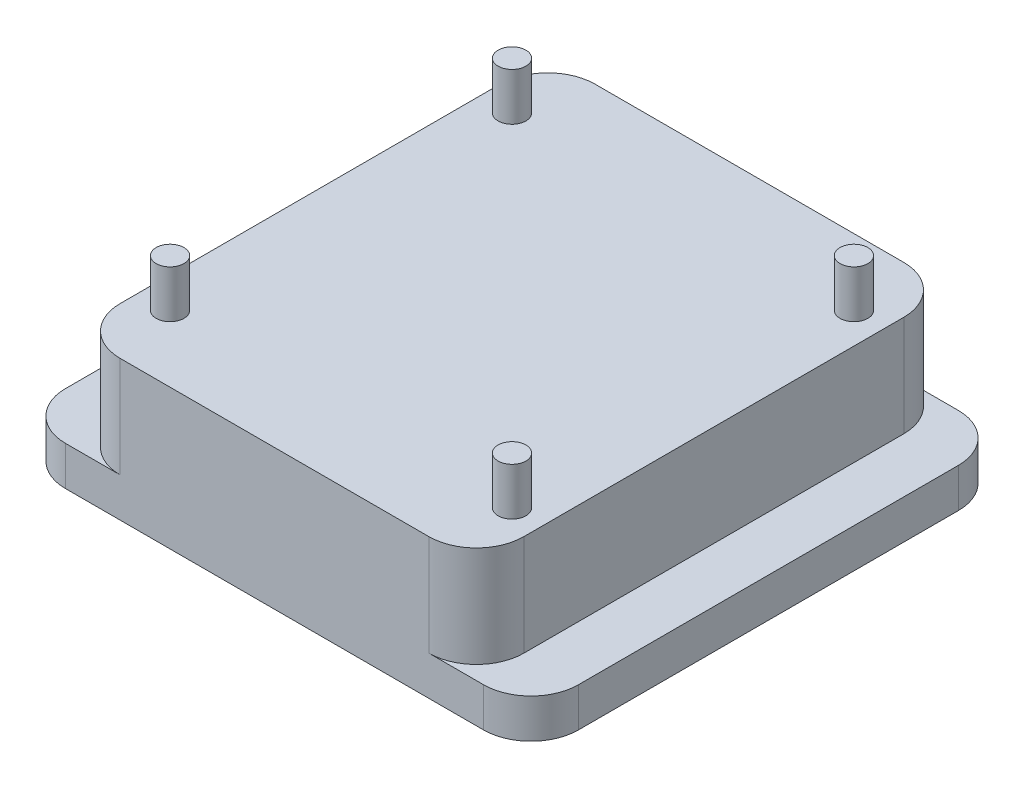
SolidWorks part; units mm, degrees
ref_plane "Front Plane" through (0, 0, 0) normal (0, 0, 1) x (1, 0, 0)
ref_plane "Top Plane" through (0, 0, 0) normal (0, 1, 0) x (1, 0, 0)
ref_plane "Right Plane" through (0, 0, 0) normal (1, 0, 0) x (0, 0, -1)
sketch "Sketch1" plane through (0, 0, 0) normal (0, 0, 1) x (1, 0, 0)
  line L1 (-27.432, -2.0955) -> (27.432, -2.0955)
  line L2 (-27.432, -2.0955) -> (-27.432, 2.0955)
  line L3 (-27.432, 2.0955) -> (27.432, 2.0955)
  line L4 (27.432, -2.0955) -> (27.432, 2.0955)
  line L5 (-27.432, -2.0955) -> (27.432, 2.0955) construction
  line L6 (-27.432, 2.0955) -> (27.432, -2.0955) construction
  line L7 (-21.59, 2.0955) -> (21.59, 2.0955)
  line L8 (-21.59, 2.0955) -> (-21.59, 5.2705)
  line L9 (-21.59, 5.2705) -> (21.59, 5.2705)
  line L10 (21.59, 2.0955) -> (21.59, 5.2705)
  line L11 (-21.59, 5.2705) -> (21.59, 5.2705)
  line L12 (-21.59, 5.2705) -> (-21.59, 12.8905)
  line L13 (-21.59, 12.8905) -> (21.59, 12.8905)
  line L14 (21.59, 5.2705) -> (21.59, 12.8905)
  point P0 (0, 0)
  point P10 (0, 5.2705)
  point P11 (0, 12.8905)
  dimension "D1" = 54.864
  dimension "D2" = 4.191
  dimension "D3" = 43.18
  dimension "D4" = 3.175
  dimension "D5" = 43.18
  dimension "D6" = 7.62
extrude "Boss-Extrude1" add sketch "Sketch1" along normal blind 50.8 contours L11 L14 L13 L12 L9 | L3 L10 L9 L8 | L1 L4 L3 L2
sketch "Sketch2" plane through (0, 12.8905, 0) normal (0, 1, 0) x (1, 0, 0)
  line L0 (-21.59, -50.8) -> (-21.59, 0) construction
  line L1 (-18.288, -7.112) -> (18.288, -7.112) construction
  line L2 (-18.288, -7.112) -> (-18.288, -43.688) construction
  line L3 (-18.288, -43.688) -> (18.288, -43.688) construction
  line L4 (18.288, -7.112) -> (18.288, -43.688) construction
  line L5 (-21.59, 0) -> (21.59, 0) construction
  circle A0 centre (-18.288, -7.112) radius 1.4859
  circle A1 centre (18.288, -7.112) radius 1.4859
  circle A2 centre (18.288, -43.688) radius 1.4859
  circle A3 centre (-18.288, -43.688) radius 1.4859
  point P4 (-18.288, -25.4)
  point P5 (-21.59, -25.4)
  point P6 (0, 0)
  point P10 (0, -7.112)
  dimension "D3" = 2.9718
  dimension "D4" = 2.9718
  dimension "D5" = 2.9718
  dimension "D6" = 2.9718
  dimension "D1" = 36.576
  dimension "D2" = 36.576
extrude "Boss-Extrude2" add sketch "Sketch2" along normal blind 5.08
fillet "Fillet1" radius 5.08 4 edges at (-21.59, 7.493, 0) (21.59, 7.493, 0) (21.59, 7.493, 50.8) (-21.59, 7.493, 50.8)
fillet "Fillet2" radius 5.08 4 edges at (-27.432, 0, 0) (-27.432, 0, 50.8) (27.432, 0, 0) (27.432, 0, 50.8)
